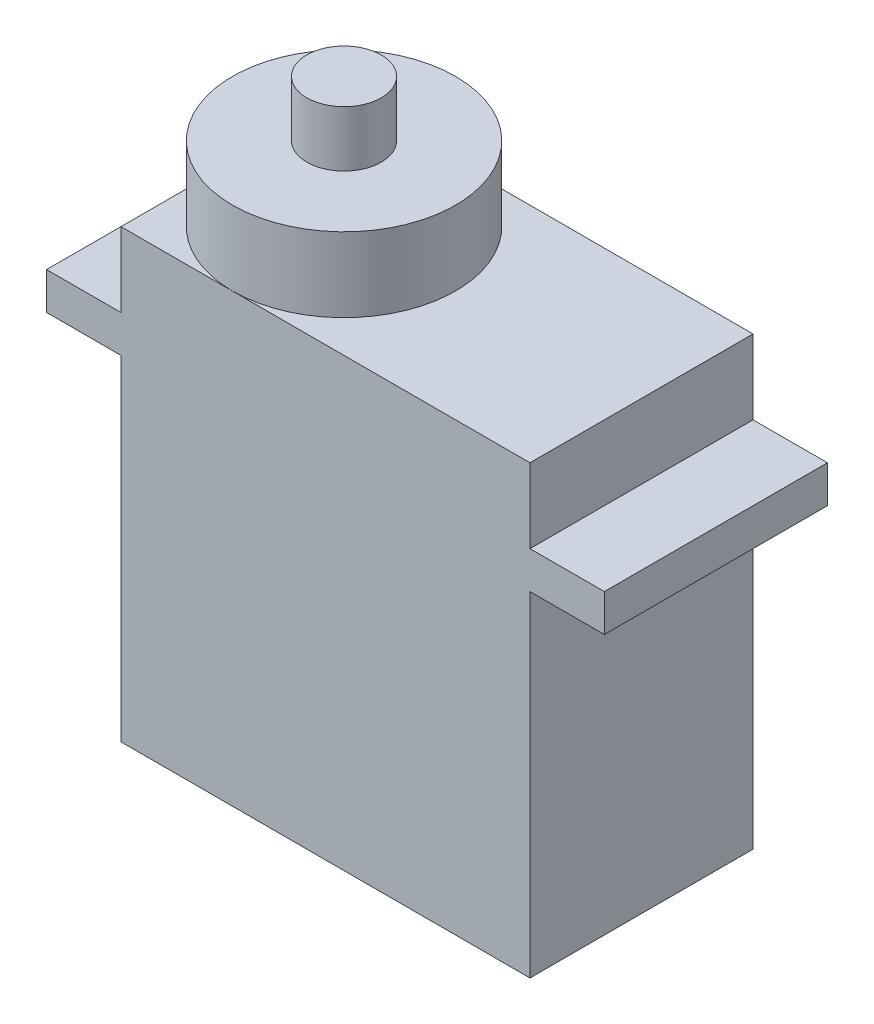
SolidWorks part; units mm, degrees
ref_plane "Front Plane" through (0, 0, 0) normal (0, 0, 1) x (1, 0, 0)
ref_plane "Top Plane" through (0, 0, 0) normal (0, 1, 0) x (1, 0, 0)
ref_plane "Right Plane" through (0, 0, 0) normal (1, 0, 0) x (0, 0, -1)
sketch "Sketch1" plane through (0, 0, 0) normal (0, 0, 1) x (1, 0, 0)
  line L1 (-11, -12) -> (11, -12)
  line L2 (-11, -12) -> (-11, 12)
  line L3 (-11, 12) -> (11, 12)
  line L4 (11, -12) -> (11, 12)
  line L5 (-11, -12) -> (11, 12) construction
  line L6 (-11, 12) -> (11, -12) construction
  point P0 (0, 0)
  dimension "D1" = 24
  dimension "D2" = 22
extrude "Boss-Extrude1" add sketch "Sketch1" along normal blind 12
sketch "Sketch2" plane through (-11, 0, 0) normal (-1, 0, 0) x (0, 0, 1)
  line L0 (0, 12) -> (0, -12) construction
  line L1 (0, 8) -> (12, 8)
  line L2 (0, 8) -> (0, 6)
  line L3 (0, 6) -> (12, 6)
  line L4 (12, 8) -> (12, 6)
  line L5 (12, 12) -> (12, -12) construction
  line L6 (12, 12) -> (0, 12) construction
  dimension "D1" = 4
  dimension "D2" = 2
extrude "Boss-Extrude2" add sketch "Sketch2" against normal blind 30 from offset 4
sketch "Sketch3" plane through (0, 12, 0) normal (0, 1, 0) x (1, 0, 0)
  line L0 (-11, -12) -> (-11, 0) construction
  line L1 (11, -12) -> (-11, -12) construction
  circle A0 centre (-5, -6) radius 6
  dimension "D1" = 12
  dimension "D2" = 6
  dimension "D3" = 6
extrude "Boss-Extrude3" add sketch "Sketch3" along normal blind 4
sketch "Sketch4" plane through (0, 16, 0) normal (0, 1, 0) x (1, 0, 0)
  circle A0 centre (-5, -6) radius 2
  arc A1 (-5, -12) -> (-5, 0) centre (-5, -6) ccw construction
  dimension "D1" = 4
extrude "Boss-Extrude4" add sketch "Sketch4" along normal blind 3
